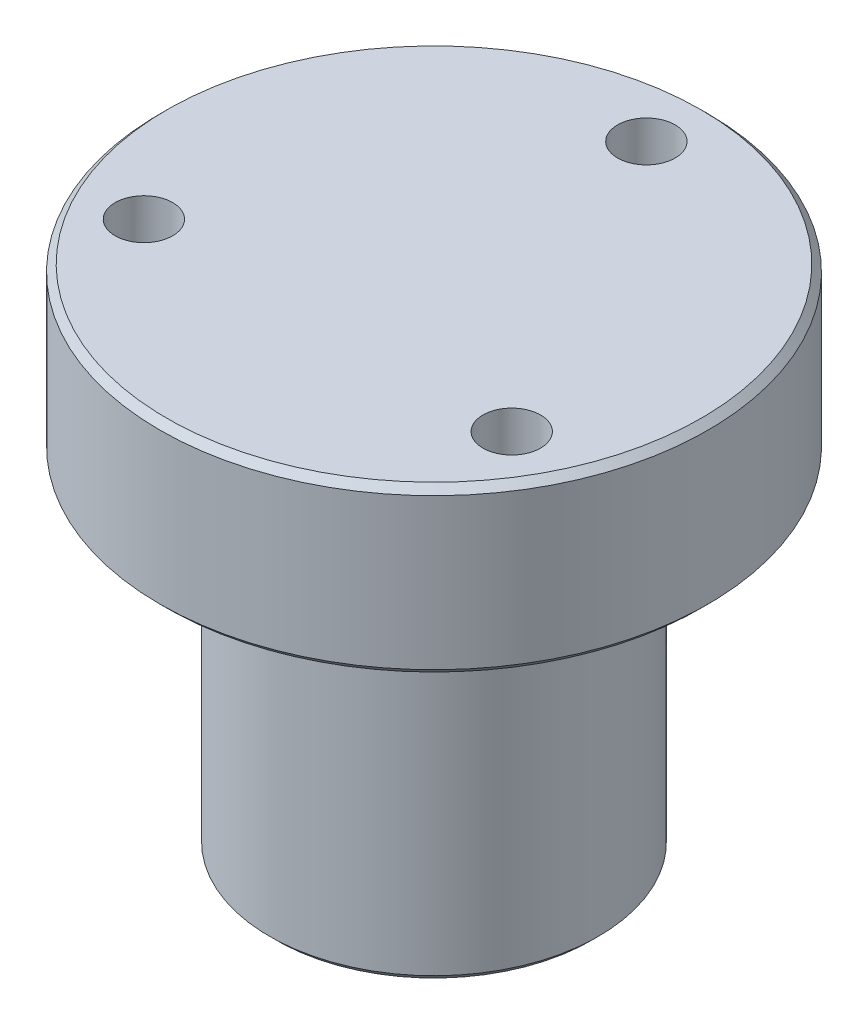
SolidWorks part; units mm, degrees
ref_plane "Front Plane" through (0, 0, 0) normal (0, 0, 1) x (1, 0, 0)
ref_plane "Top Plane" through (0, 0, 0) normal (0, 1, 0) x (1, 0, 0)
ref_plane "Right Plane" through (0, 0, 0) normal (1, 0, 0) x (0, 0, -1)
sketch "Sketch1" plane through (0, 0, 0) normal (0, 0, 1) x (1, 0, 0)
  line L0 (0, 0) -> (0, 37)
  line L1 (0, 37) -> (19.5, 37)
  line L2 (20, 36.5) -> (20, 25.5)
  line L3 (19.5, 25) -> (12, 25)
  line L4 (12, 25) -> (12, 0.5)
  line L5 (11.5, 0) -> (0, 0)
  line L6 (0, 0) -> (0, 53.1455) construction
  line L7 (19.5, 37) -> (20, 36.5)
  line L8 (20, 25.5) -> (19.5, 25)
  line L9 (12, 0.5) -> (11.5, 0)
  point P4 (20, 37)
  point P5 (20, 25)
  point P7 (12, 0)
  dimension "D1" = 20
  dimension "D2" = 12
  dimension "D3" = 37
  dimension "D4" = 12
revolve "Revolve1" add sketch "Sketch1" angle 360 about L6
sketch "Sketch2" plane through (0, 37, 0) normal (0, 1, 0) x (1, 0, 0)
  circle A0 centre (0, 15.5) radius 2.1006
  circle A1 centre (13.4234, -7.75) radius 2.1006
  circle A2 centre (-13.4234, -7.75) radius 2.1006
  point P9 (0, 0)
  dimension "D1" = 4.2012
  dimension "D2" = 15.5
  dimension "D3" = 3
extrude "Cut-Extrude1" cut sketch "Sketch2" against normal through all
